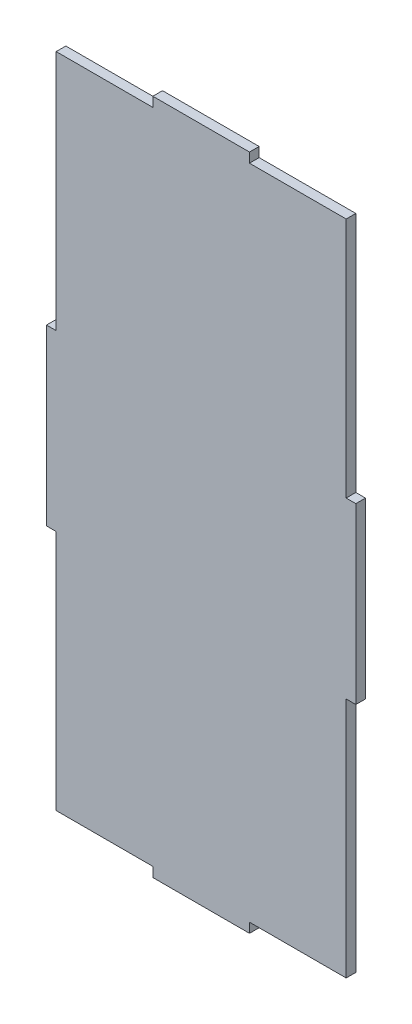
SolidWorks part; units mm, degrees
ref_plane "Front Plane" through (0, 0, 0) normal (0, 0, 1) x (1, 0, 0)
ref_plane "Top Plane" through (0, 0, 0) normal (0, 1, 0) x (1, 0, 0)
ref_plane "Right Plane" through (0, 0, 0) normal (1, 0, 0) x (0, 0, -1)
sketch "Sketch1" plane through (0, 0, 0) normal (0, 0, 1) x (1, 0, 0)
  line L1 (-444.0624, 402.5086) -> (-228.1624, 402.5086)
  line L2 (-444.0624, 402.5086) -> (-444.0624, -54.6914)
  line L3 (-444.0624, -54.6914) -> (-228.1624, -54.6914)
  line L4 (-228.1624, 402.5086) -> (-228.1624, -54.6914)
  line L5 (-444.0624, 402.5086) -> (-228.1624, -54.6914) construction
  line L6 (-444.0624, -54.6914) -> (-228.1624, 402.5086) construction
  point P0 (-336.1124, 173.9086)
  dimension "D1" = 215.9
  dimension "D2" = 457.2
extrude "Boss-Extrude1" add sketch "Sketch1" along normal blind 6.35
ref_plane "Plane1" through (-228.1624, -54.6914, 6.35) normal (1, 0, 0) x (0, 0, -1)
sketch "Sketch3" plane through (0, 0, 6.35) normal (0, 0, 1) x (1, 0, 0)
  line L0 (-444.0624, -41.9914) -> (-367.8624, -41.9914)
  line L1 (-444.0624, 402.5086) -> (-444.0624, -54.6914) construction
  line L5 (-444.0624, -54.6914) -> (-228.1624, -54.6914) construction
  line L6 (-367.8624, -41.9914) -> (-367.8624, -54.6914)
extrude "Cut-Extrude1" cut sketch "Sketch3" against normal through all and the other way through all flip side to cut
sketch "Sketch4" plane through (0, 0, 6.35) normal (0, 0, 1) x (1, 0, 0)
  line L0 (-228.1624, -41.9914) -> (-304.3624, -41.9914)
  line L1 (-228.1624, -54.6914) -> (-228.1624, 402.5086) construction
  line L2 (-304.3624, -41.9914) -> (-304.3624, -54.6914)
  line L3 (-367.8624, -54.6914) -> (-228.1624, -54.6914) construction
extrude "Cut-Extrude2" cut sketch "Sketch4" against normal through all and the other way through all
sketch "Sketch5" plane through (0, 0, 6.35) normal (0, 0, 1) x (1, 0, 0)
  line L2 (-367.8624, -48.3414) -> (-304.3624, -48.3414)
  line L3 (-367.8624, -54.6914) -> (-367.8624, -41.9914) construction
  line L4 (-304.3624, -54.6914) -> (-304.3624, -41.9914) construction
extrude "Cut-Extrude3" cut sketch "Sketch5" against normal through all and the other way through all flip side to cut
sketch "Sketch6" plane through (0, 0, 6.35) normal (0, 0, 1) x (1, 0, 0)
  line L0 (-444.0624, 389.8086) -> (-367.8624, 389.8086)
  line L1 (-444.0624, 402.5086) -> (-444.0624, -41.9914) construction
  line L3 (-367.8624, 389.8086) -> (-367.8624, 402.5086)
  line L4 (-228.1624, 402.5086) -> (-444.0624, 402.5086) construction
extrude "Cut-Extrude4" cut sketch "Sketch6" against normal through all and the other way through all
sketch "Sketch7" plane through (0, 0, 6.35) normal (0, 0, 1) x (1, 0, 0)
  line L0 (-228.1624, 389.8086) -> (-304.3624, 389.8086)
  line L1 (-228.1624, -41.9914) -> (-228.1624, 402.5086) construction
  line L2 (-304.3624, 389.8086) -> (-304.3624, 402.5086)
  line L3 (-228.1624, 402.5086) -> (-367.8624, 402.5086) construction
extrude "Cut-Extrude6" cut sketch "Sketch7" against normal through all and the other way through all flip side to cut
sketch "Sketch8" plane through (0, 0, 6.35) normal (0, 0, 1) x (1, 0, 0)
  line L5 (-367.8624, 402.5086) -> (-367.8624, 389.8086) construction
  line L7 (-304.3624, 402.5086) -> (-304.3624, 389.8086) construction
  line L8 (-304.3624, 396.1586) -> (-367.8624, 396.1586)
extrude "Cut-Extrude7" cut sketch "Sketch8" against normal through all and the other way through all flip side to cut
sketch "Sketch9" plane through (0, 0, 6.35) normal (0, 0, 1) x (1, 0, 0)
  line L2 (-240.8624, -41.9914) -> (-240.8624, 116.7586)
  line L3 (-304.3624, -41.9914) -> (-228.1624, -41.9914) construction
  line L5 (-240.8624, 116.7586) -> (-228.1624, 116.7586)
  line L6 (-228.1624, -41.9914) -> (-228.1624, 389.8086) construction
extrude "Cut-Extrude9" cut sketch "Sketch9" against normal through all and the other way through all flip side to cut
sketch "Sketch10" plane through (0, 0, 6.35) normal (0, 0, 1) x (1, 0, 0)
  line L0 (-240.8624, 389.8086) -> (-240.8624, 231.0586)
  line L1 (-304.3624, 389.8086) -> (-228.1624, 389.8086) construction
  line L2 (-240.8624, 231.0586) -> (-228.1624, 231.0586)
  line L3 (-228.1624, 116.7586) -> (-228.1624, 389.8086) construction
extrude "Cut-Extrude12" cut sketch "Sketch10" against normal through all and the other way through all
sketch "Sketch12" plane through (0, 0, 6.35) normal (0, 0, 1) x (1, 0, 0)
  line L2 (-234.5124, 231.0586) -> (-234.5124, 116.7586)
  line L3 (-228.1624, 231.0586) -> (-240.8624, 231.0586) construction
  line L4 (-228.1624, 116.7586) -> (-240.8624, 116.7586) construction
extrude "Cut-Extrude13" cut sketch "Sketch12" against normal through all
sketch "Sketch13" plane through (0, 0, 6.35) normal (0, 0, 1) x (1, 0, 0)
  line L0 (-431.3624, -41.9914) -> (-431.3624, 116.7586)
  line L1 (-367.8624, -41.9914) -> (-444.0624, -41.9914) construction
  line L2 (-444.0624, 116.7586) -> (-431.3624, 116.7586)
  line L3 (-444.0624, 389.8086) -> (-444.0624, -41.9914) construction
extrude "Cut-Extrude14" cut sketch "Sketch13" against normal through all and the other way through all flip side to cut
sketch "Sketch14" plane through (0, 0, 6.35) normal (0, 0, 1) x (1, 0, 0)
  line L0 (-431.3624, 389.8086) -> (-431.3624, 231.0586)
  line L1 (-367.8624, 389.8086) -> (-444.0624, 389.8086) construction
  line L2 (-431.3624, 231.0586) -> (-444.0624, 231.0586)
  line L3 (-444.0624, 389.8086) -> (-444.0624, 116.7586) construction
extrude "Cut-Extrude15" cut sketch "Sketch14" against normal through all and the other way through all flip side to cut
ref_plane "Plane3" through (-444.0624, 116.7586, 6.35) normal (0, -1, 0) x (-1, 0, 0)
sketch "Sketch16" plane through (0, 0, 6.35) normal (0, 0, 1) x (1, 0, 0)
  line L2 (-437.7124, 231.0586) -> (-437.7124, 116.7586)
  line L3 (-444.0624, 231.0586) -> (-431.3624, 231.0586) construction
extrude "Cut-Extrude16" cut sketch "Sketch16" against normal through all and the other way through all flip side to cut
